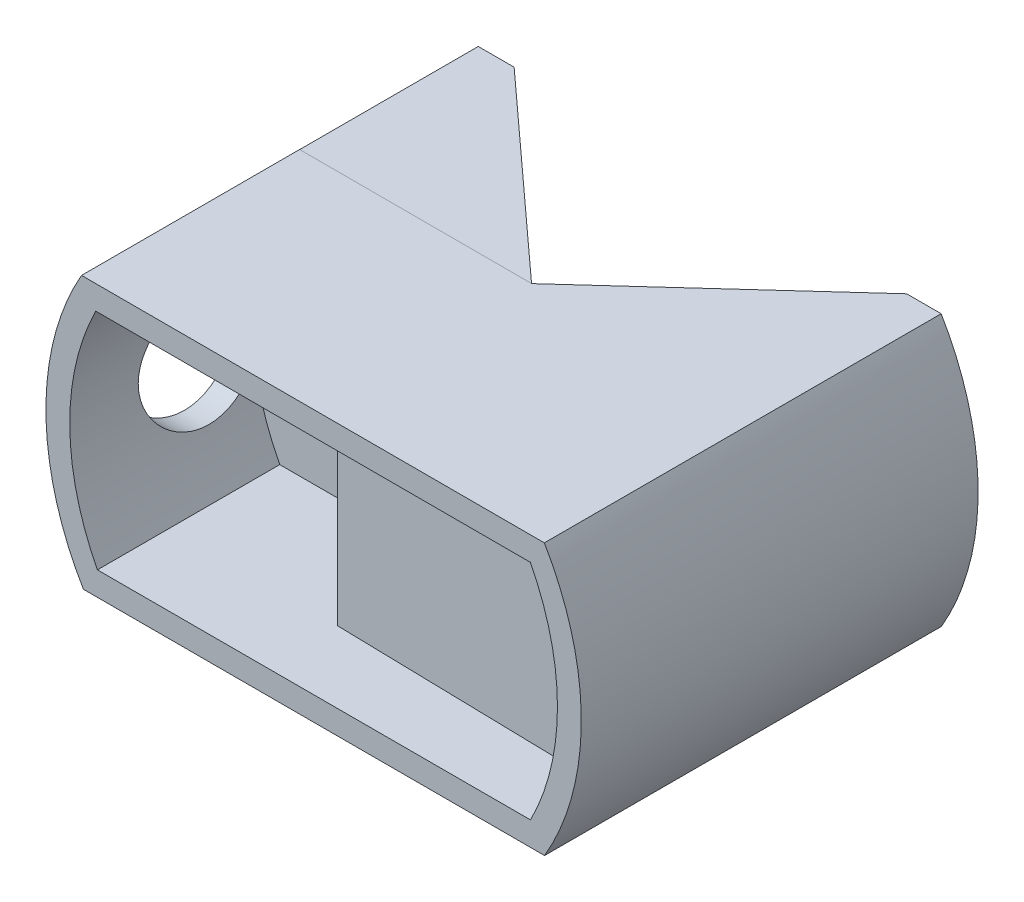
SolidWorks part; units mm, degrees
ref_plane "Front Plane" through (0, 0, 0) normal (0, 0, 1) x (1, 0, 0)
ref_plane "Top Plane" through (0, 0, 0) normal (0, 1, 0) x (1, 0, 0)
ref_plane "Right Plane" through (0, 0, 0) normal (1, 0, 0) x (0, 0, -1)
sketch "Sketch1" plane through (0, 0, -12.295) normal (0, 0, -1) x (-1, 0, 0)
  line L4 (-169.3691, -111.49) -> (-130.6784, -111.4894)
  line L5 (-130.5221, -88.7593) -> (-169.3507, -88.7786)
  line L6 (-169.3691, -111.49) -> (-130.6784, -111.4894)
  line L7 (-130.5221, -88.7593) -> (-169.3507, -88.7786)
  arc A4 (-130.6784, -111.4894) -> (-130.5221, -88.7593) centre (-150.13, -99.99) ccw
  arc A5 (-169.3507, -88.7786) -> (-169.3691, -111.49) centre (-150.04, -100.15) ccw
  arc A6 (-130.6784, -111.4894) -> (-130.5221, -88.7593) centre (-150.13, -99.99) ccw
  arc A7 (-169.3507, -88.7786) -> (-169.3691, -111.49) centre (-150.04, -100.15) ccw
  dimension "D1" = 2.5
extrude "Boss-Extrude1" add sketch "Sketch1" against normal offset from surface (15.295 mm away) 3
sketch "Sketch2" plane through (0, 0, 3) normal (0, 0, 1) x (1, 0, 0)
  line L4 (168.1711, -90.7781) -> (131.7176, -90.7599)
  line L5 (131.855, -109.4894) -> (168.1876, -109.49)
  line L6 (168.1711, -90.7781) -> (131.7176, -90.7599)
  line L7 (131.855, -109.4894) -> (168.1876, -109.49)
  arc A4 (168.1876, -109.49) -> (168.1711, -90.7781) centre (150.04, -100.15) ccw
  arc A5 (131.7176, -90.7599) -> (131.855, -109.4894) centre (150.13, -99.99) ccw
  arc A6 (168.1876, -109.49) -> (168.1711, -90.7781) centre (150.04, -100.15) ccw
  arc A7 (131.7176, -90.7599) -> (131.855, -109.4894) centre (150.13, -99.99) ccw
  dimension "D1" = 2
extrude "Cut-Extrude1" cut sketch "Sketch2" against normal through all
sketch "Sketch4" plane through (0, 0, -12.295) normal (0, 0, -1) x (-1, 0, 0)
  line L2 (-169.3691, -111.49) -> (-130.6784, -111.4894)
  line L3 (-130.5221, -88.7593) -> (-169.3507, -88.7786)
  line L4 (-169.3691, -111.49) -> (-130.6784, -111.4894)
  line L5 (-130.5221, -88.7593) -> (-169.3507, -88.7786)
  arc A2 (-169.3507, -88.7786) -> (-169.3691, -111.49) centre (-150.04, -100.15) ccw
  arc A3 (-130.6784, -111.4894) -> (-130.5221, -88.7593) centre (-150.13, -99.99) ccw
  arc A4 (-169.3507, -88.7786) -> (-169.3691, -111.49) centre (-150.04, -100.15) ccw
  arc A5 (-130.6784, -111.4894) -> (-130.5221, -88.7593) centre (-150.13, -99.99) ccw
  dimension "D1" = 0
extrude "floor" add sketch "Sketch4" along normal blind 3
sketch "Sketch6" plane through (0, 0, -12.295) normal (0, 0, 1) x (1, 0, 0)
  line L0 (146.5, -90.7672) -> (146.5, -108.9896)
  line L1 (167.88, -108.99) -> (132.1612, -108.9894) construction
  line L2 (131.855, -109.4894) -> (168.1876, -109.49)
  line L3 (168.1711, -90.7781) -> (131.7176, -90.7599)
  line L6 (145, -95.6) -> (145, -104.4) construction
  line L7 (168.1711, -90.7781) -> (146.5, -90.7672)
  line L8 (168.1876, -109.49) -> (146.5, -108.9896)
  arc A2 (168.1876, -109.49) -> (168.1711, -90.7781) centre (150.04, -100.15) ccw
  arc A3 (131.7176, -90.7599) -> (131.855, -109.4894) centre (150.13, -99.99) ccw
  arc A4 (168.1876, -109.49) -> (168.1711, -90.7781) centre (150.04, -100.15) ccw
  dimension "D2" = 1.5
  dimension "D1" = 0
extrude "Boss-Extrude4" add sketch "Sketch6" along normal offset from surface (9.785 mm away) 1
sketch "Sketch7" plane through (0, 0, 0) normal (1, 0, 0) x (0, 0, -1)
  circle A0 centre (7.995, -100) radius 5.25
  point P2 (7.995, -100)
  dimension "D1" = 10.5
extrude "Cut-Extrude3" cut sketch "Sketch7" along normal up to surface (129.5336 mm away)
sketch "Sketch9" plane through (0, 0, -15.295) normal (0, 0, -1) x (-1, 0, 0)
  line L0 (-169.3507, -88.7786) -> (-130.6784, -111.4894) construction
  line L1 (-130.5221, -88.7593) -> (-169.3691, -111.49) construction
  line L2 (-169.3691, -111.49) -> (-130.6784, -111.4894)
  line L3 (-130.5221, -88.7593) -> (-169.3507, -88.7786)
  line L4 (-169.3691, -111.49) -> (-130.6784, -111.4894)
  line L5 (-130.5221, -88.7593) -> (-169.3507, -88.7786)
  arc A2 (-169.3507, -88.7786) -> (-169.3691, -111.49) centre (-150.04, -100.15) ccw
  arc A3 (-130.6784, -111.4894) -> (-130.5221, -88.7593) centre (-150.13, -99.99) ccw
  arc A4 (-169.3507, -88.7786) -> (-169.3691, -111.49) centre (-150.04, -100.15) ccw
  arc A5 (-130.6784, -111.4894) -> (-130.5221, -88.7593) centre (-150.13, -99.99) ccw
  point P0 (-149.9882, -100.1495)
  point P5 (0, 0)
  point P8 (0, 0)
  point P9 (0, 0)
  point P10 (0, 0)
  point P11 (0, 0)
  point P12 (0, 0)
  dimension "D1" = 0
ref_plane "Plane1" through (0, 0, -15.295) normal (0, 0, -1) x (-1, 0, 0)
ref_plane "Plane2" through (149.9898, -0.0025, 0) normal (-1, 0, 0) x (0, 0, 1)
sketch "Sketch11" plane through (-0.0443, -88.694, 0) normal (0.0005, 1, 0) x (1, -0.0005, 0)
  line L0 (150.0382, 15.295) -> (166.5001, 30.295)
  line L1 (166.5001, 30.295) -> (172.5001, 30.295)
  line L2 (172.5001, 30.295) -> (172.5001, 15.295)
  line L3 (172.5001, 15.295) -> (169.395, 15.295) construction
  line L4 (12.5019, 15.295) -> (-12.5019, 15.295) construction
  line L5 (172.5001, 15.295) -> (150.0382, 15.295)
  line L12 (172.5001, -3) -> (172.5001, 15.295) construction
  point P4 (0, 0)
  point P10 (165.6596, 30.295)
  point P11 (166.1635, 30.295)
  point P12 (169.395, 29.147)
  point P13 (169.395, 30.295)
  point P14 (169.395, 30.295)
  point P15 (169.395, 30.295)
  dimension "D1" = 15
  dimension "D2" = 6
extrude "Boss-Extrude5" add sketch "Sketch11" against normal up to surface (22.7099 mm away)
mirror "Mirror1" about plane through (149.9898, -0.0025, 0) normal (-1, 0, 0) of "Boss-Extrude5"
sketch "Sketch14" plane through (0, 0, 3) normal (0, 0, 1) x (1, 0, 0)
  line L2 (169.3507, -88.7786) -> (130.5221, -88.7593)
  line L3 (130.6784, -111.4894) -> (169.3691, -111.49)
  line L4 (169.3507, -88.7786) -> (130.5221, -88.7593)
  line L5 (130.6784, -111.4894) -> (169.3691, -111.49)
  arc A2 (169.3691, -111.49) -> (169.3507, -88.7786) centre (150.04, -100.15) ccw
  arc A3 (130.5221, -88.7593) -> (130.6784, -111.4894) centre (150.13, -99.99) ccw
  arc A4 (169.3691, -111.49) -> (169.3507, -88.7786) centre (150.04, -100.15) ccw
  arc A5 (130.5221, -88.7593) -> (130.6784, -111.4894) centre (150.13, -99.99) ccw
  dimension "D1" = 0
extrude "Cut-Extrude4" cut sketch "Sketch14" against normal up to surface (33.295 mm away) flip side to cut up to face at (169.4501, -100.1344, -30.295)
